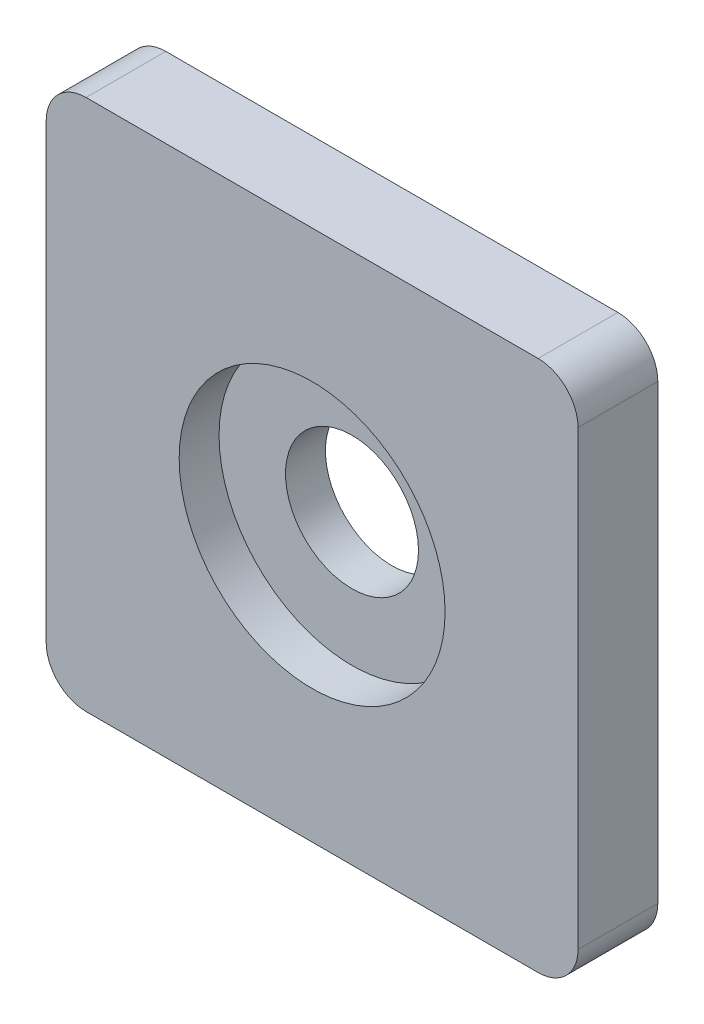
SolidWorks part; units mm, degrees
material "CA"
ref_plane "Plan de face" through (0, 0, 0) normal (0, 0, 1) x (1, 0, 0)
ref_plane "Plan de dessus" through (0, 0, 0) normal (0, 1, 0) x (1, 0, 0)
ref_plane "Plan de droite" through (0, 0, 0) normal (1, 0, 0) x (0, 0, -1)
sketch "Esquisse1" plane through (0, 0, 0) normal (0, 0, 1) x (1, 0, 0)
  line L1 (-8.5, -10) -> (8.5, -10)
  line L2 (-10, -8.5) -> (-10, 8.5)
  line L3 (-8.5, 10) -> (8.5, 10)
  line L4 (10, -8.5) -> (10, 8.5)
  line L5 (-10, -10) -> (10, 10) construction
  line L6 (-10, 10) -> (10, -10) construction
  circle A0 centre (0, 0) radius 2.5
  arc A1 (-8.5, -10) -> (-10, -8.5) centre (-8.5, -8.5) cw
  arc A2 (8.5, -10) -> (10, -8.5) centre (8.5, -8.5) ccw
  arc A3 (8.5, 10) -> (10, 8.5) centre (8.5, 8.5) cw
  arc A4 (-10, 8.5) -> (-8.5, 10) centre (-8.5, 8.5) cw
  point P0 (0, 0)
  dimension "D2" = 5
  dimension "D3" = 1.5
  dimension "D1" = 20
extrude "Boss.-Extru.1" add sketch "Esquisse1" along normal mid plane 3
sketch "Esquisse2" plane through (0, 0, 1.5) normal (0, 0, 1) x (1, 0, 0)
  circle A0 centre (0, 0) radius 5
  dimension "D1" = 10
extrude "Enlèv. mat.-Extru.1" cut sketch "Esquisse2" against normal up to surface (1.5 mm away)
